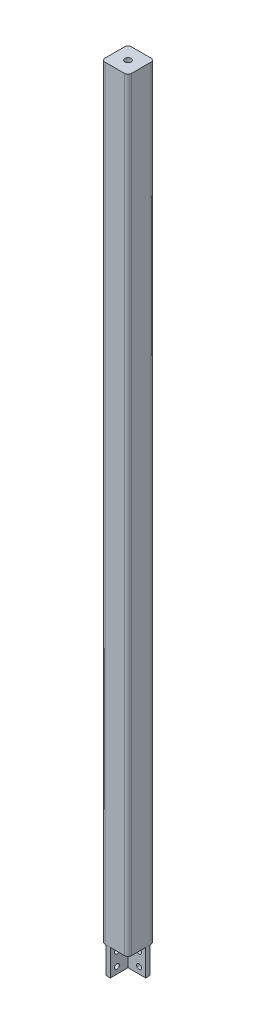
SolidWorks part; units mm, degrees
material "A3钢"
ref_plane "前视基准面" through (0, 0, 0) normal (0, 0, 1) x (1, 0, 0)
ref_plane "上视基准面" through (0, 0, 0) normal (0, 1, 0) x (1, 0, 0)
ref_plane "右视基准面" through (0, 0, 0) normal (1, 0, 0) x (0, 0, -1)
sketch "草图1" plane through (0, 0, 0) normal (0, 0, 1) x (1, 0, 0)
  line L0 (0, 1720) -> (0, 0)
  dimension "D1" = 1720
other "方管 60 X 60 X 4.0(1)"
ref_plane "基准面1" through (0, 1720, 0) normal (0, -1, 0) x (1, 0, 0)
sketch "Sketch1" plane through (0, 1720, 0) normal (0, -1, 0) x (1, 0, 0)
  line L0 (-22, -26) -> (22, -26)
  line L1 (-26, -22) -> (-26, 22)
  line L2 (22, 26) -> (-22, 26)
  line L3 (26, 22) -> (26, -22)
  line L4 (-22, -30) -> (22, -30)
  line L5 (-30, -22) -> (-30, 22)
  line L6 (22, 30) -> (-22, 30)
  line L7 (30, 22) -> (30, -22)
  line L8 (-30, 0) -> (-26, 0) construction
  line L9 (-26, 0) -> (26, 0) construction
  line L10 (26, 0) -> (30, 0) construction
  line L12 (0, 30) -> (0, 26) construction
  line L13 (0, 26) -> (0, -26) construction
  line L14 (0, -26) -> (0, -30) construction
  arc A0 (30, 22) -> (22, 30) centre (22, 22) ccw
  arc A1 (22, -30) -> (30, -22) centre (22, -22) ccw
  arc A2 (-30, -22) -> (-22, -30) centre (-22, -22) ccw
  arc A3 (-22, 30) -> (-30, 22) centre (-22, 22) ccw
  arc A4 (-22, 26) -> (-26, 22) centre (-22, 22) ccw
  arc A5 (26, 22) -> (22, 26) centre (22, 22) ccw
  arc A6 (22, -26) -> (26, -22) centre (22, -22) ccw
  arc A7 (-26, -22) -> (-22, -26) centre (-22, -22) ccw
  point P2 (-30, 30)
  point P33 (-30, -30)
  point P34 (30, -30)
  point P36 (30, 30)
  point P37 (0, 0)
  dimension "D1" = 8
  dimension "Thickness" = 4
  dimension "V_leg" = 60
  dimension "H_leg" = 60
sketch "草图4" plane through (0, 1720, 0) normal (0, 1, 0) x (1, 0, 0)
  line L4 (30, -22) -> (30, 22)
  line L5 (22, 30) -> (-22, 30)
  line L6 (-30, 22) -> (-30, -22)
  line L7 (-22, -30) -> (22, -30)
  line L8 (30, -22) -> (30, 22)
  line L9 (22, 30) -> (-22, 30)
  line L10 (-30, 22) -> (-30, -22)
  line L11 (-22, -30) -> (22, -30)
  arc A4 (22, -30) -> (30, -22) centre (22, -22) ccw
  arc A5 (30, 22) -> (22, 30) centre (22, 22) ccw
  arc A6 (-22, 30) -> (-30, 22) centre (-22, 22) ccw
  arc A7 (-30, -22) -> (-22, -30) centre (-22, -22) ccw
  arc A8 (22, -30) -> (30, -22) centre (22, -22) ccw
  arc A9 (30, 22) -> (22, 30) centre (22, 22) ccw
  arc A10 (-22, 30) -> (-30, 22) centre (-22, 22) ccw
  arc A11 (-30, -22) -> (-22, -30) centre (-22, -22) ccw
  dimension "D1" = 0
extrude "凸台-拉伸1" add sketch "草图4" along normal blind 10
sketch "草图5" plane through (0, 1730, 0) normal (0, 1, 0) x (1, 0, 0)
  circle A0 centre (0, 0) radius 10
  dimension "D1" = 20
hole_wizard "M16 螺纹孔1" positions "3D草图1" profile "草图6" tap size "M16" standard "GB" end condition through all
sketch3d "3D草图1"
  point P0 (0, 1730, 0)
sketch "草图6" plane through (0, 1730, 0) normal (1, 0, 0) x (0, 0, 1)
  line L0 (0, 0) -> (0, 1730)
  line L1 (0, 1730) -> (7, 1730)
  line L2 (7, 1730) -> (7, 0)
  line L5 (7, 0) -> (0, 0)
  line L11 (0, -6.35) -> (0, 107.95) construction
  dimension "通孔螺纹孔钻头直径" = 14
  dimension "通孔螺纹孔钻头深度" = 1730
cosmetic thread "孔螺蚊线1" parameters "D2"=16
sketch "草图15" plane through (0, 0, 0) normal (0, -1, 0) x (1, 0, 0)
  line L0 (-26, 22) -> (-26, -22) construction
  line L1 (-22, -26) -> (22, -26) construction
  line L2 (26, -22) -> (26, 22) construction
  line L3 (22, 26) -> (-22, 26) construction
  line L4 (-26, 22) -> (-26, -22)
  line L5 (-22, -26) -> (22, -26)
  line L6 (26, -22) -> (26, 22)
  line L7 (22, 26) -> (-22, 26)
  arc A0 (-26, -22) -> (-22, -26) centre (-22, -22) ccw construction
  arc A1 (-22, 26) -> (-26, 22) centre (-22, 22) ccw construction
  arc A2 (22, -26) -> (26, -22) centre (22, -22) ccw construction
  arc A3 (26, 22) -> (22, 26) centre (22, 22) ccw construction
  arc A4 (-26, -22) -> (-22, -26) centre (-22, -22) ccw
  arc A5 (-22, 26) -> (-26, 22) centre (-22, 22) ccw
  arc A6 (22, -26) -> (26, -22) centre (22, -22) ccw
  arc A7 (26, 22) -> (22, 26) centre (22, 22) ccw
extrude "凸台-拉伸4" add sketch "草图15" against normal blind 10 separate body
sketch "草图19" plane through (0, 0, 0) normal (0, -1, 0) x (1, 0, 0)
  line L0 (-20, 30) -> (-20, -20)
  line L1 (-20, -20) -> (30, -20)
  line L2 (30, -10) -> (-10, -10)
  line L3 (-10, -10) -> (-10, 30)
  line L4 (-10, 30) -> (-20, 30)
  line L5 (30, -10) -> (30, -20)
  line L8 (-22, -30) -> (22, -30) construction
  line L9 (-30, 22) -> (-30, -22) construction
  dimension "D1" = 10
  dimension "D2" = 10
  dimension "D3" = 10
  dimension "D4" = 10
  dimension "D5" = 50
  dimension "D6" = 50
extrude "凸台-拉伸5" add sketch "草图19" along normal blind 60 separate body
sketch "草图20" plane through (0, 0, -20) normal (0, 0, -1) x (-1, 0, 0)
  line L0 (-15, -15) -> (-15, -45) construction
  line L1 (20, 0) -> (-30, 0) construction
  line L2 (20, -60) -> (-30, -60) construction
  line L3 (20, -60) -> (20, 0) construction
  dimension "D1" = 15
  dimension "D2" = 15
  dimension "D3" = 35
hole_wizard "Ø11.0 (11) 直径孔1" positions "3D草图2" profile "草图22" hole size "Ø11.0" standard "GB" end condition through all
sketch3d "3D草图2"
  point P0 (15, -15, -20)
  point P3 (15, -45, -20)
sketch "草图22" plane through (15, -15, -20) normal (1, 0, 0) x (0, 1, 0)
  line L0 (0, 0) -> (0, 50)
  line L1 (0, 50) -> (5.5, 50)
  line L2 (5.5, 50) -> (5.5, 0)
  line L5 (5.5, 0) -> (0, 0)
  line L11 (0, -6.35) -> (0, 107.95) construction
  dimension "通孔孔直径" = 11
  dimension "通孔孔深度" = 50
sketch "草图23" plane through (-10, 0, 0) normal (1, 0, 0) x (0, 0, -1)
  line L0 (-15, -45) -> (-15, -15) construction
  line L1 (20, -60) -> (20, 0) construction
  line L2 (10, -60) -> (-30, -60) construction
  line L3 (10, 0) -> (-30, 0) construction
  dimension "D1" = 35
  dimension "D2" = 15
  dimension "D3" = 15
hole_wizard "Ø11.0 (11) 直径孔2" positions "3D草图3" profile "草图24" hole size "Ø11.0" standard "GB" end condition through all
sketch3d "3D草图3"
  point P0 (-10, -45, 15)
  point P3 (-10, -15, 15)
sketch "草图24" plane through (-10, -45, 15) normal (0, 1, 0) x (0, 0, -1)
  line L0 (0, 0) -> (0, 20)
  line L1 (0, 20) -> (5.5, 20)
  line L2 (5.5, 20) -> (5.5, 0)
  line L5 (5.5, 0) -> (0, 0)
  line L11 (0, -6.35) -> (0, 107.95) construction
  dimension "通孔孔直径" = 11
  dimension "通孔孔深度" = 20
